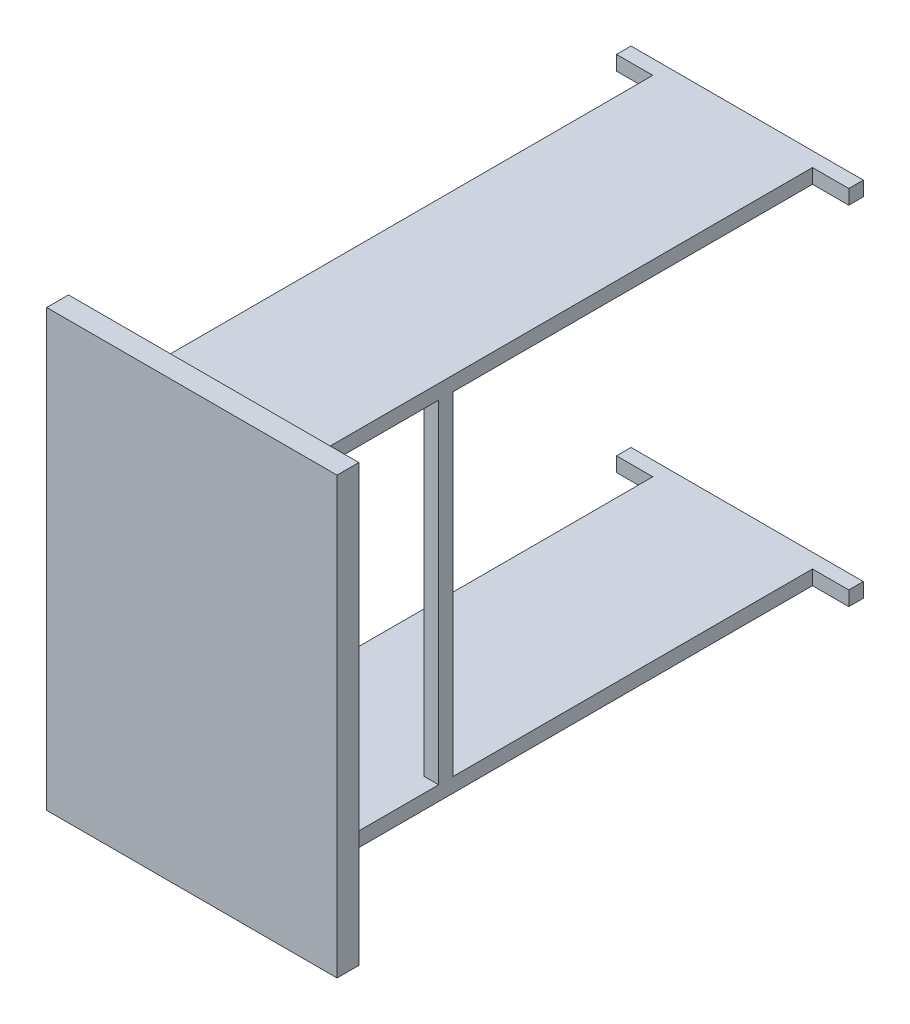
SolidWorks part; units mm, degrees
ref_plane "Alzado" through (0, 0, 0) normal (0, 0, 1) x (1, 0, 0)
ref_plane "Planta" through (0, 0, 0) normal (0, 1, 0) x (1, 0, 0)
ref_plane "Vista lateral" through (0, 0, 0) normal (1, 0, 0) x (0, 0, -1)
sketch "Croquis1" plane through (0, 0, 0) normal (0, 0, 1) x (1, 0, 0)
  line L1 (-200, 300) -> (200, 300)
  line L2 (-200, 300) -> (-200, -300)
  line L3 (-200, -300) -> (200, -300)
  line L4 (200, 300) -> (200, -300)
  line L5 (-200, 300) -> (200, -300) construction
  line L6 (-200, -300) -> (200, 300) construction
  point P0 (0, 0)
  dimension "D1" = 600
  dimension "D2" = 400
extrude "Saliente-Extruir1" add sketch "Croquis1" along normal blind 30
sketch "Croquis3" plane through (0, 0, 0) normal (0, 0, -1) x (-1, 0, 0)
  line L0 (-200, -300) -> (-200, 300) construction
  line L1 (-160, 249.4717) -> (160, 249.4717)
  line L2 (-160, 249.4717) -> (-160, 229.4717)
  line L3 (-160, 229.4717) -> (160, 229.4717)
  line L4 (160, 249.4717) -> (160, 229.4717)
  line L5 (-160, 249.4717) -> (160, 229.4717) construction
  line L6 (-160, 229.4717) -> (160, 249.4717) construction
  line L7 (200, 300) -> (200, -300) construction
  point P0 (0, 239.4717)
  dimension "D1" = 20
  dimension "D2" = 40
  dimension "D3" = 40
extrude "Saliente-Extruir2" add sketch "Croquis3" along normal blind 735
mirror "Simetría1" about plane through (0, 0, 0) normal (0, 1, 0) of "Saliente-Extruir2"
sketch "Croquis4" plane through (0, -249.4717, 0) normal (0, -1, 0) x (1, 0, 0)
  line L0 (-200, 0) -> (200, 0) construction
  line L1 (-160, -20) -> (-110, -20)
  line L2 (-160, -20) -> (-160, -715)
  line L3 (-160, -715) -> (-110, -715)
  line L4 (-110, -20) -> (-110, -715)
  line L5 (-160, -20) -> (-110, -715) construction
  line L6 (-160, -715) -> (-110, -20) construction
  line L7 (-160, -735) -> (160, -735) construction
  line L8 (-160, -735) -> (-160, 0) construction
  line L9 (0, 0) -> (0, -217.2457) construction
  line L10 (160, -715) -> (110, -715)
  line L11 (110, -20) -> (110, -715)
  line L12 (160, -20) -> (110, -20)
  line L13 (160, -20) -> (160, -715)
  point P0 (-135, -367.5)
  dimension "D1" = 20
  dimension "D2" = 20
  dimension "D3" = 0
  dimension "D4" = 50
extrude "Cortar-Extruir1" cut sketch "Croquis4" against normal through all
sketch "Croquis5" plane through (0, 229.4717, 0) normal (0, -1, 0) x (1, 0, 0)
  line L0 (-110, -20) -> (-110, -715) construction
  line L1 (-110, -200) -> (-90, -200)
  line L2 (-110, -200) -> (-110, -220)
  line L3 (-110, -220) -> (-90, -220)
  line L4 (-90, -200) -> (-90, -220)
  line L5 (-110, -200) -> (-90, -220) construction
  line L6 (-110, -220) -> (-90, -200) construction
  line L7 (-160, -20) -> (-110, -20) construction
  point P0 (-100, -210)
  dimension "D1" = 20
  dimension "D2" = 20
  dimension "D3" = 0
  dimension "D4" = 180
extrude "Saliente-Extruir3" add sketch "Croquis5" along normal up to next (458.9435 mm away)
mirror "Simetría2" about plane through (0, 0, 0) normal (1, 0, 0) of "Saliente-Extruir3"
